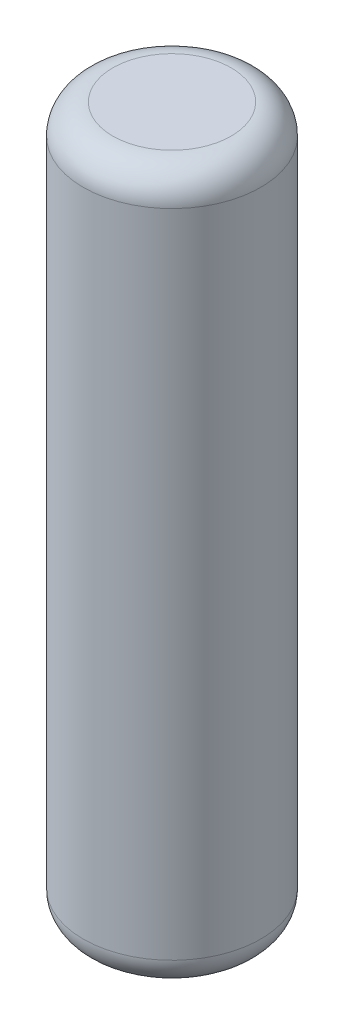
SolidWorks part; units mm, degrees
material "Cast Alloy Steel"
ref_plane "Front Plane" through (0, 0, 0) normal (0, 0, 1) x (1, 0, 0)
ref_plane "Top Plane" through (0, 0, 0) normal (0, 1, 0) x (1, 0, 0)
ref_plane "Right Plane" through (0, 0, 0) normal (1, 0, 0) x (0, 0, -1)
sketch "Sketch1" plane through (0, 0, 0) normal (0, 1, 0) x (1, 0, 0)
  circle A0 centre (0, 0) radius 30
  dimension "D1" = 60
extrude "Boss-Extrude1" add sketch "Sketch1" along normal blind 240
fillet "Fillet1" radius 10 2 edges at (0, 0, 30) (0, 240, 30)
